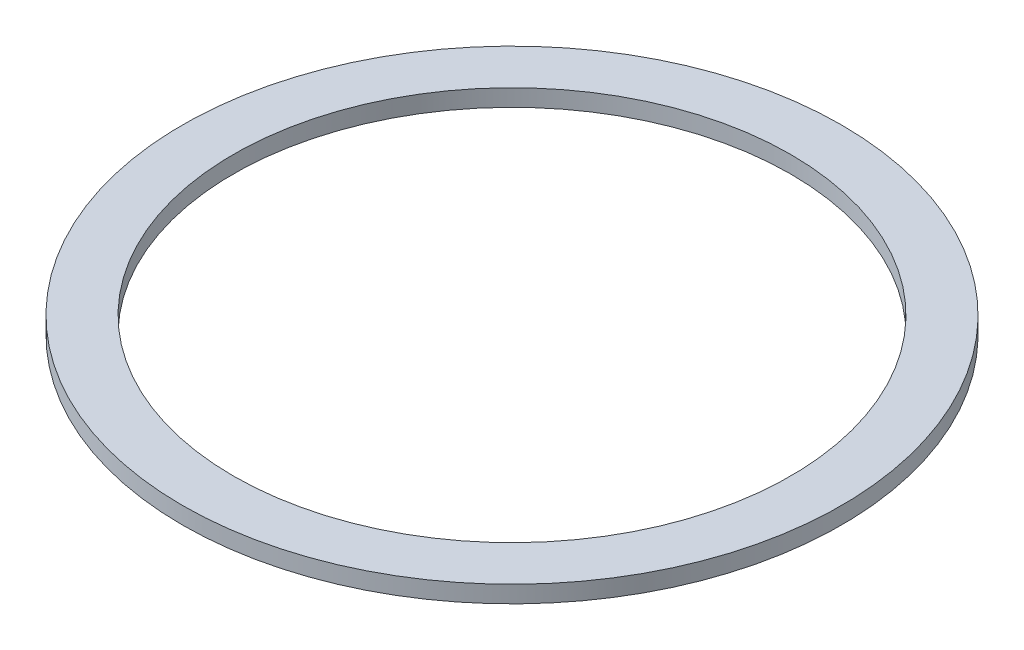
SolidWorks part; units mm, degrees
ref_plane "Front Plane" through (0, 0, 0) normal (0, 0, 1) x (1, 0, 0)
ref_plane "Top Plane" through (0, 0, 0) normal (0, 1, 0) x (1, 0, 0)
ref_plane "Right Plane" through (0, 0, 0) normal (1, 0, 0) x (0, 0, -1)
sketch "Sketch1" plane through (0, 0, 0) normal (0, 1, 0) x (1, 0, 0)
  line L0 (16.4, 0) -> (19.4, 0) construction
  circle A0 centre (0, 0) radius 16.4
  circle A1 centre (0, 0) radius 19.4
  dimension "D1" = 32.8
  dimension "D2" = 3
extrude "Boss-Extrude1" add sketch "Sketch1" along normal blind 1
